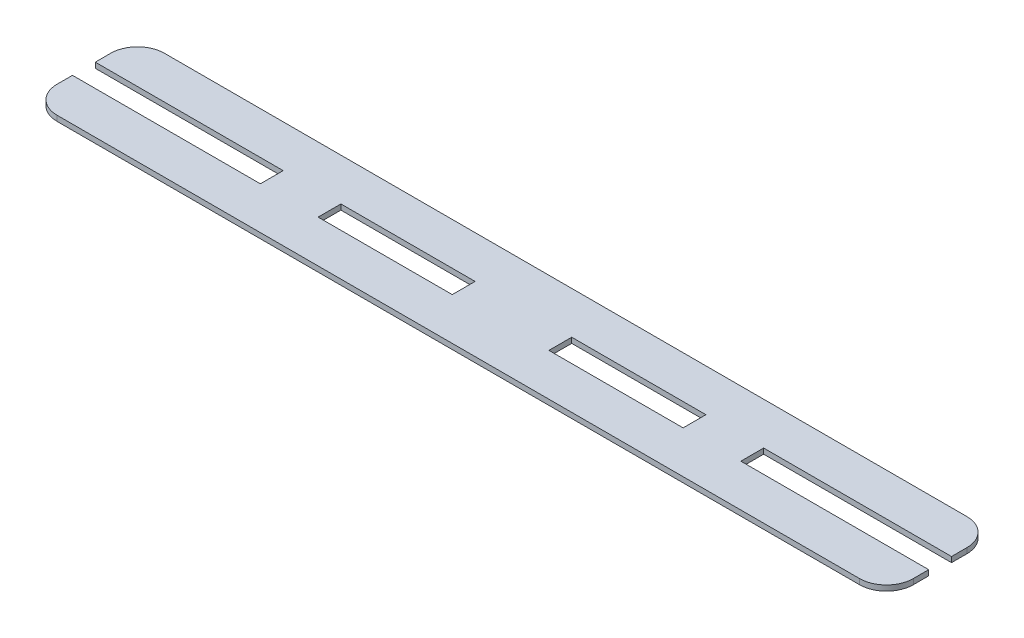
SolidWorks part; units mm, degrees
ref_plane "Front Plane" through (0, 0, 0) normal (0, 0, 1) x (1, 0, 0)
ref_plane "Top Plane" through (0, 0, 0) normal (0, 1, 0) x (1, 0, 0)
ref_plane "Right Plane" through (0, 0, 0) normal (1, 0, 0) x (0, 0, -1)
sketch "Sketch1" plane through (0, 0, 0) normal (0, 1, 0) x (1, 0, 0)
  line L1 (0, 0) -> (319, 0)
  line L2 (0, 0) -> (0, -40)
  line L3 (0, -40) -> (319, -40)
  line L4 (319, 0) -> (319, -40)
  dimension "D1" = 40
  dimension "D2" = 319
extrude "Boss-Extrude1" add sketch "Sketch1" along normal blind 2
sketch "Sketch2" plane through (0, 2, 0) normal (0, 1, 0) x (1, 0, 0)
  line L0 (0, -20) -> (319, -20) construction
  line L1 (0, 0) -> (0, -40) construction
  line L2 (319, -40) -> (319, 0) construction
  line L4 (0, -24.25) -> (70, -24.25)
  line L5 (0, -24.25) -> (0, -15.75)
  line L6 (0, -15.75) -> (70, -15.75)
  line L7 (70, -24.25) -> (70, -15.75)
  point P10 (0, -20)
  dimension "D1" = 70
  dimension "D2" = 8.5
extrude "Cut-Extrude1" cut sketch "Sketch2" against normal through all
sketch "Sketch3" plane through (0, 2, 0) normal (0, 1, 0) x (1, 0, 0)
  line L0 (319, -20) -> (0, -20) construction
  line L1 (319, -40) -> (319, 0) construction
  line L2 (0, 0) -> (0, -15.75) construction
  line L3 (91.5, -15.75) -> (141.5, -15.75)
  line L4 (91.5, -15.75) -> (91.5, -24.25)
  line L5 (91.5, -24.25) -> (141.5, -24.25)
  line L6 (141.5, -15.75) -> (141.5, -24.25)
  point P8 (91.5, -20)
  point P11 (116.5, -15.75)
  dimension "D1" = 116.5
  dimension "D2" = 8.5
  dimension "D3" = 50
extrude "Cut-Extrude2" cut sketch "Sketch3" against normal through all
ref_plane "Plane1" through (159.5, 0, 0) normal (-1, 0, 0) x (0, 0, 1)
mirror "Mirror1" about plane through (159.5, 0, 0) normal (-1, 0, 0) of "Cut-Extrude2", "Cut-Extrude1"
fillet "Fillet1" radius 10 4 edges at (0, 1, 40) (0, 1, 0) (319, 1, 40) (319, 1, 0)
